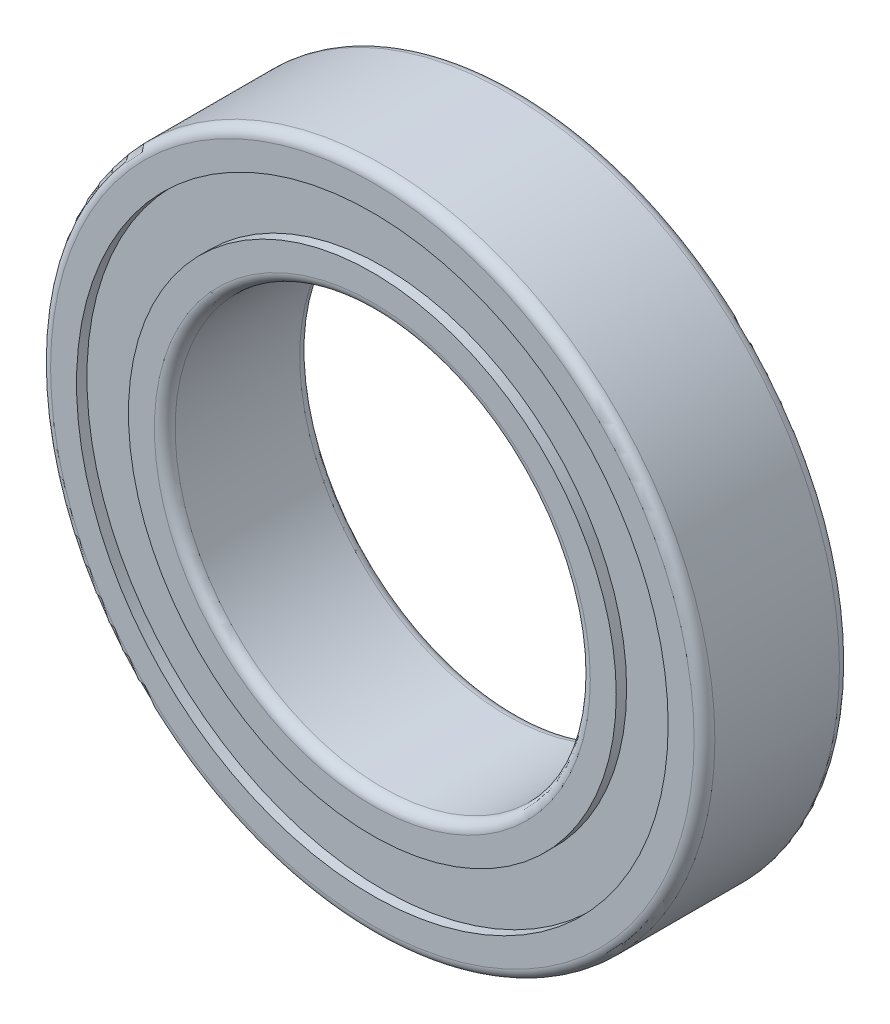
SolidWorks part; units mm, degrees
ref_plane "Front Plane" through (0, 0, 0) normal (0, 0, 1) x (1, 0, 0)
ref_plane "Top Plane" through (0, 0, 0) normal (0, 1, 0) x (1, 0, 0)
ref_plane "Right Plane" through (0, 0, 0) normal (1, 0, 0) x (0, 0, -1)
sketch "Sketch1" plane through (0, 0, 0) normal (0, 0, 1) x (1, 0, 0)
  circle A0 centre (80, 28.2573) radius 10
  circle A1 centre (80, 28.2573) radius 16
extrude "Boss-Extrude1" add sketch "Sketch1" along normal blind 7
fillet "Fillet1" radius 0.5
sketch "Sketch2" plane through (0, 0, 0) normal (0, 0, -1) x (-1, 0, 0)
  circle A0 centre (-80, 28.2573) radius 11.75
  circle A1 centre (-80, 28.2573) radius 14.25
extrude "Cut-Extrude1" cut sketch "Sketch2" against normal blind 0.5 contours A1 A0
sketch "Sketch3" plane through (0, 0, 7) normal (0, 0, 1) x (1, 0, 0)
  circle A0 centre (80, 28.2573) radius 11.75 construction
  circle A1 centre (80, 28.2573) radius 14.25
  circle A2 centre (80, 28.2573) radius 14.25
  circle A3 centre (80, 28.2573) radius 11.75
  dimension "D1" = 0
extrude "Cut-Extrude2" cut sketch "Sketch3" against normal blind 0.5
